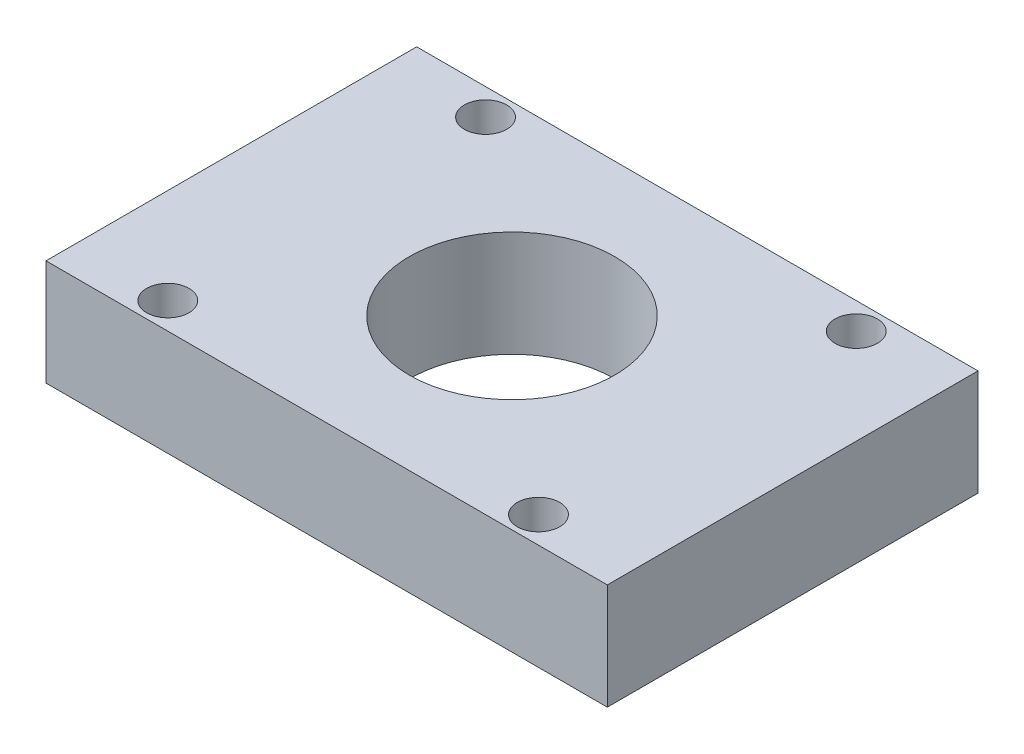
SolidWorks part; units mm, degrees
ref_plane "Front Plane" through (0, 0, 0) normal (0, 0, 1) x (1, 0, 0)
ref_plane "Top Plane" through (0, 0, 0) normal (0, 1, 0) x (1, 0, 0)
ref_plane "Right Plane" through (0, 0, 0) normal (1, 0, 0) x (0, 0, -1)
sketch "Sketch1" plane through (0, 0, 0) normal (0, 1, 0) x (1, 0, 0)
  line L1 (-26.5, 17.5) -> (26.5, 17.5)
  line L2 (-26.5, 17.5) -> (-26.5, -17.5)
  line L3 (-26.5, -17.5) -> (26.5, -17.5)
  line L4 (26.5, 17.5) -> (26.5, -17.5)
  line L5 (-26.5, 17.5) -> (26.5, -17.5) construction
  line L6 (-26.5, -17.5) -> (26.5, 17.5) construction
  point P0 (0, 0)
  dimension "D1" = 53
  dimension "D2" = 35
extrude "Boss-Extrude1" add sketch "Sketch1" along normal blind 10
sketch "Sketch2" plane through (0, 10, 0) normal (0, 1, 0) x (1, 0, 0)
  line L0 (-17.5, 15) -> (17.5, 15) construction
  line L1 (17.5, 15) -> (17.5, -15) construction
  line L2 (17.5, -15) -> (-17.5, -15) construction
  line L3 (-17.5, -15) -> (-17.5, 15) construction
  line L4 (-17.5, 15) -> (17.5, -15) construction
  circle A0 centre (-17.5, 15) radius 2
  circle A1 centre (17.5, 15) radius 2
  circle A2 centre (-17.5, -15) radius 2
  circle A3 centre (17.5, -15) radius 2
  circle A4 centre (0, 0) radius 9.6992
  point P3 (0, 0)
  dimension "D1" = 30
  dimension "35" = 35
extrude "Cut-Extrude1" cut sketch "Sketch2" against normal through all
